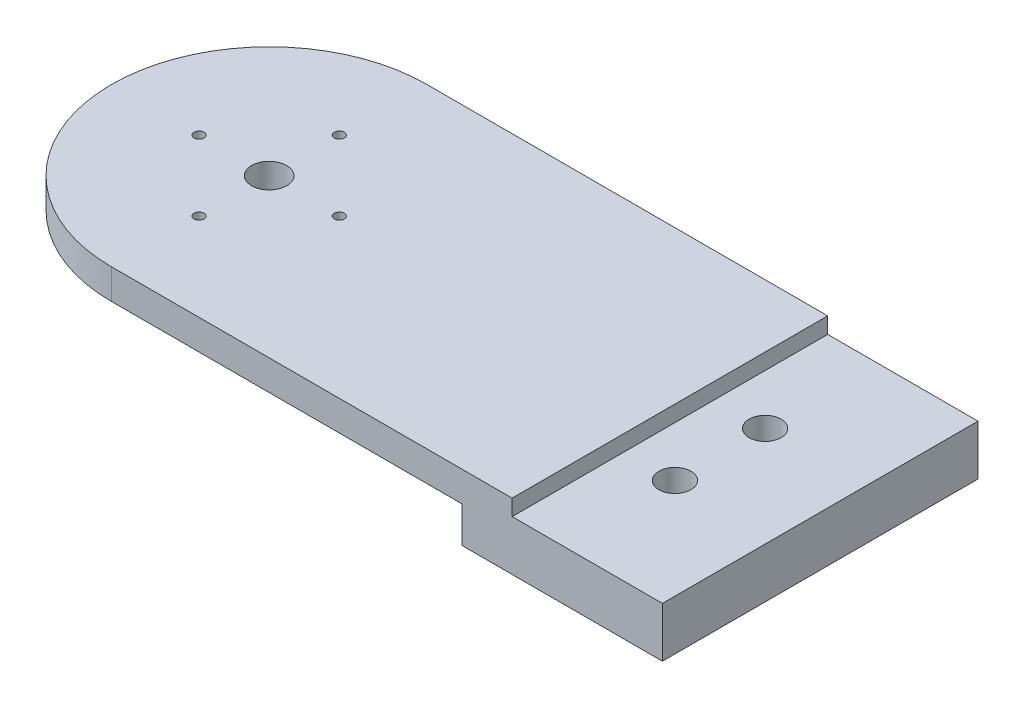
SolidWorks part; units mm, degrees
ref_plane "前视基准面" through (0, 0, 0) normal (0, 0, 1) x (1, 0, 0)
ref_plane "上视基准面" through (0, 0, 0) normal (0, 1, 0) x (1, 0, 0)
ref_plane "右视基准面" through (0, 0, 0) normal (1, 0, 0) x (0, 0, -1)
sketch "草图1" plane through (0, 0, 0) normal (0, 1, 0) x (1, 0, 0)
  line L0 (0, -15.75) -> (55, -15.75)
  line L1 (55, -15.75) -> (55, 15.75)
  line L2 (55, 15.75) -> (0, 15.75)
  arc A0 (0, 15.75) -> (0, -15.75) centre (0, 0) ccw
  dimension "D1" = 31.5
  dimension "D2" = 55
extrude "凸台-拉伸1" add sketch "草图1" along normal blind 3
sketch "草图3" plane through (0, 0, 0) normal (0, -1, 0) x (1, 0, 0)
  line L0 (0, 15.75) -> (55, 15.75) construction
  line L1 (35, 15.75) -> (55, 15.75)
  line L2 (35, 15.75) -> (35, -15.75)
  line L3 (35, -15.75) -> (55, -15.75)
  line L4 (55, 15.75) -> (55, -15.75)
  dimension "D1" = 20
extrude "凸台-拉伸2" add sketch "草图3" along normal blind 2
sketch "草图4" plane through (0, 0, 0) normal (0, -1, 0) x (1, 0, 0)
  circle A4 centre (0, 0) radius 7 construction
  circle A5 centre (0, 7) radius 0.5
  circle A6 centre (7, 0) radius 0.5
  circle A7 centre (0, -7) radius 0.5
  circle A8 centre (-7, 0) radius 0.5
  dimension "D1" = 1
  dimension "D2" = 1
  dimension "D3" = 1
  dimension "D4" = 1
  dimension "D5" = 14
extrude "切除-拉伸1" cut sketch "草图4" against normal blind 10
sketch "草图5" plane through (0, -2, 0) normal (0, -1, 0) x (1, 0, 0)
  line L0 (55, 0) -> (31.5597, 0) construction
  line L1 (55, -15.75) -> (55, 15.75) construction
  circle A0 centre (45, -4.5) radius 1.6
  circle A1 centre (45, 4.5) radius 1.6
  dimension "D1" = 9
  dimension "D2" = 10
  dimension "D3" = 3.2
extrude "切除-拉伸2" cut sketch "草图5" against normal blind 10
sketch "草图6" plane through (0, 0, 0) normal (0, -1, 0) x (1, 0, 0)
  circle A0 centre (0, 0) radius 1.75
  dimension "D1" = 3.5
extrude "切除-拉伸3" cut sketch "草图6" against normal blind 17
sketch "草图7" plane through (0, 0, 0) normal (0, -1, 0) x (1, 0, 0)
  line L3 (35, -15.75) -> (35, 15.75)
  line L4 (35, 15.75) -> (0, 15.75)
  line L5 (0, -15.75) -> (35, -15.75)
  line L6 (35, -15.75) -> (35, 15.75)
  line L7 (35, 15.75) -> (0, 15.75)
  line L8 (0, -15.75) -> (35, -15.75)
  arc A1 (0, 15.75) -> (0, -15.75) centre (0, 0) ccw
  arc A2 (0, 15.75) -> (0, -15.75) centre (0, 0) ccw
  dimension "D1" = 0
extrude "切除-拉伸4" cut sketch "草图7" against normal blind 1.6
sketch "草图8" plane through (0, 1.6, 0) normal (0, -1, 0) x (1, 0, 0)
  line L3 (0, -15.75) -> (35, -15.75)
  line L4 (35, -15.75) -> (35, 15.75)
  line L5 (35, 15.75) -> (0, 15.75)
  line L6 (0, -15.75) -> (35, -15.75)
  line L7 (35, -15.75) -> (35, 15.75)
  line L8 (35, 15.75) -> (0, 15.75)
  arc A1 (0, 15.75) -> (0, -15.75) centre (0, 0) ccw
  arc A2 (0, 15.75) -> (0, -15.75) centre (0, 0) ccw
  dimension "D1" = 0
extrude "凸台-拉伸3" add sketch "草图8" against normal blind 3
sketch "草图9" plane through (35, 0, 0) normal (1, 0, 0) x (0, 0, -1)
  line L1 (-15.75, 4.6) -> (15.75, 4.6)
  line L2 (-15.75, 4.6) -> (-15.75, 3)
  line L3 (-15.75, 3) -> (15.75, 3)
  line L4 (15.75, 4.6) -> (15.75, 3)
extrude "凸台-拉伸4" add sketch "草图9" along normal blind 3
sketch "草图10" plane through (0, 1.6, 0) normal (0, -1, 0) x (1, 0, 0)
  circle A0 centre (0, 0) radius 1.75
  circle A1 centre (0, 7) radius 0.5
  circle A2 centre (7, 0) radius 0.5
  circle A3 centre (0, -7) radius 0.5
  circle A4 centre (-7, 0) radius 0.5
  dimension "D1" = 3.5
  dimension "D4" = 1
  dimension "D5" = 1
  dimension "D6" = 1
  dimension "D7" = 1
  dimension "D2" = 7
  dimension "D3" = 7
  dimension "D8" = 7
  dimension "D9" = 7
extrude "切除-拉伸5" cut sketch "草图10" against normal blind 10
sketch "草图12" plane through (0, 1.6, 0) normal (0, -1, 0) x (1, 0, 0)
  circle A0 centre (0, 0) radius 10
  dimension "D1" = 20
extrude "凸台-拉伸6" add sketch "草图12" along normal blind 1.6
sketch "草图13" plane through (38, 0, 0) normal (1, 0, 0) x (0, 0, -1)
  line L1 (-15.75, 4.6) -> (15.75, 4.6)
  line L2 (-15.75, 4.6) -> (-15.75, 3)
  line L3 (-15.75, 3) -> (15.75, 3)
  line L4 (15.75, 4.6) -> (15.75, 3)
extrude "凸台-拉伸7" add sketch "草图13" along normal blind 2
sketch "草图15" plane through (0, 0, 0) normal (0, -1, 0) x (1, 0, 0)
  circle A0 centre (0, 0) radius 1.75
  circle A1 centre (7, 0) radius 0.5
  circle A2 centre (0, -7) radius 0.5
  circle A3 centre (0, 7) radius 0.5
  circle A4 centre (-7, 0) radius 0.5
  dimension "D1" = 3.5
  dimension "D2" = 1
  dimension "D3" = 1
  dimension "D4" = 1
  dimension "D5" = 1
  dimension "D6" = 7
  dimension "D7" = 7
  dimension "D8" = 7
  dimension "D9" = 7
extrude "切除-拉伸6" cut sketch "草图15" against normal blind 12
